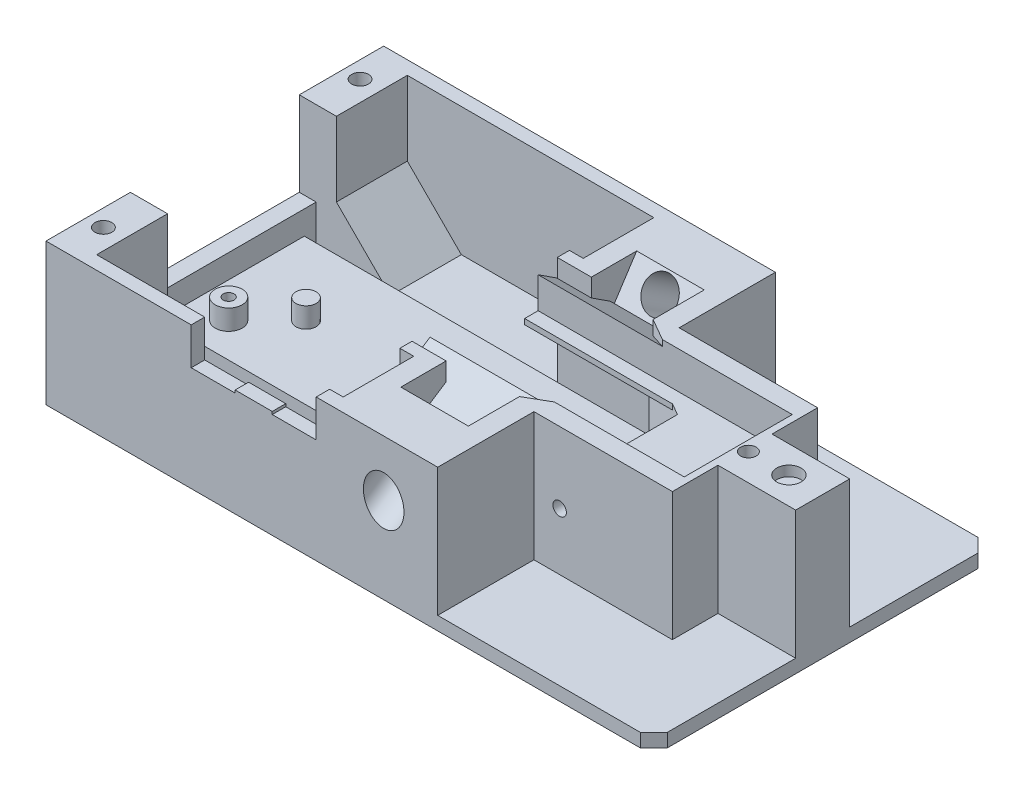
SolidWorks part; units mm, degrees
ref_plane "Front Plane" through (0, 0, 0) normal (0, 0, 1) x (1, 0, 0)
ref_plane "Top Plane" through (0, 0, 0) normal (0, 1, 0) x (1, 0, 0)
ref_plane "Right Plane" through (0, 0, 0) normal (1, 0, 0) x (0, 0, -1)
sketch "Sketch1" plane through (0, 0, 0) normal (0, 1, 0) x (1, 0, 0)
  line L0 (-111.1111, 0) -> (149.5726, 0) construction
  line L1 (0, 75.7479) -> (0, -66.1325) construction
  line L3 (-50, 25) -> (40, 25)
  line L4 (-50, 25) -> (-50, -25)
  line L5 (-50, -25) -> (40, -25)
  line L6 (40, 25) -> (40, -25)
  dimension "D1" = 50
  dimension "D2" = 40
  dimension "D3" = 50
extrude "Boss-Extrude1" add sketch "Sketch1" along normal blind 21
sketch "Sketch2" plane through (0, 21, 0) normal (0, 1, 0) x (1, 0, 0)
  line L0 (0, 0) -> (-72.5321, 0) construction
  line L1 (-44.5, 10.75) -> (3.5, 10.75)
  line L2 (-44.5, 10.75) -> (-44.5, -10.75)
  line L3 (-44.5, -10.75) -> (3.5, -10.75)
  line L4 (13.5, 5) -> (13.5, -5)
  line L5 (13.5, 5) -> (3.5, 10.75)
  line L6 (13.5, -5) -> (3.5, -10.75)
  dimension "D1" = 21.5
  dimension "D2" = 58
  dimension "D3" = 13.5
  dimension "D4" = 10
  dimension "D5" = 10
extrude "Cut-Extrude1" cut sketch "Sketch2" against normal offset from surface (16 mm away) 5 up to face at (-5, 0, 0)
sketch "Sketch3" plane through (0, 0, 0) normal (1, 0, 0) x (0, 0, -1)
  line L0 (38.5857, 3.8917) -> (0, 29) construction
  line L1 (-23.1325, 29) -> (24.9292, 29) construction
  line L2 (5, 5) -> (-5, 5) construction
  line L3 (0, 0) -> (0, 44.5037) construction
  line L4 (-25, 0) -> (25, 0) construction
  line L5 (25, 15.8341) -> (1.4181, 31.1792) construction
  line L6 (25, 9.6301) -> (-1.4181, 26.8208) construction
  line L7 (27.5121, 11.0974) -> (0, 29) construction
  line L8 (26.094, 8.9182) -> (-1.4181, 26.8208) construction
  line L9 (-18.1916, 17.5) -> (11.6037, 17.5) construction
  line L10 (7.5, -5.5044) -> (7.5, 37.9907) construction
  line L11 (28.9302, 13.2767) -> (1.4181, 31.1792) construction
  line L12 (25, 21) -> (25, 0) construction
  dimension "D1" = 24
  dimension "D4" = 12.5
  dimension "D5" = 7.5
  dimension "D2" = 2.6
  dimension "D3" = 2.6
ref_plane "Plane1" through (0, 3.8917, -38.5857) normal (0, 0.5454, 0.8382) x (1, 0, 0)
sketch "Sketch4" plane through (0, 3.8917, -38.5857) normal (0, 0.5454, 0.8382) x (1, 0, 0)
  circle A0 centre (0, 0) radius 2.5
  dimension "D1" = 5
extrude "Cut-Extrude2" cut sketch "Sketch4" along normal through all contours A0
ref_plane "Plane2" through (0, 29, 0) normal (0, 0.5454, 0.8382) x (1, 0, 0)
sketch "Sketch5" plane through (0, 29, 0) normal (0, 0.5454, 0.8382) x (1, 0, 0)
  line L0 (0, 0.0137) -> (12.9105, 0.0137) construction
  line L1 (-5, -3.0863) -> (5, -3.0863)
  line L2 (-5, -3.0863) -> (-5, 3.1137)
  line L3 (-5, 3.1137) -> (5, 3.1137)
  line L4 (5, -3.0863) -> (5, 3.1137)
  line L5 (0, -24.83) -> (0, 11.6263) construction
  line L6 (0, 0.0137) -> (0, 5.31) construction
  dimension "D1" = 6.2
  dimension "D2" = 10
extrude "Cut-Extrude3" cut sketch "Sketch5" against normal blind 19
sketch "Sketch6" plane through (0, 3.8917, -38.5857) normal (0, 0.5454, 0.8382) x (1, 0, 0)
  circle A0 centre (0, 0) radius 3
  dimension "D1" = 6
extrude "Cut-Extrude4" cut sketch "Sketch6" along normal blind 20
sketch "Sketch11" plane through (0, 5, 0) normal (0, 1, 0) x (1, 0, 0)
  line L0 (11.3, 6.265) -> (11.3, -6.265)
  line L1 (3.5, 10.75) -> (13.5, 5) construction
  line L2 (13.5, -5) -> (3.5, -10.75) construction
  line L3 (11.3, -6.265) -> (13.5, -5)
  line L4 (13.5, -5) -> (13.5, 5)
  line L6 (13.5, 5) -> (11.3, 6.265)
  line L7 (13.5, 5) -> (13.5, -5) construction
  line L8 (0, 0) -> (-46.0103, 0) construction
  circle A0 centre (-36.5, 0) radius 1.5
  dimension "D3" = 3
  dimension "D1" = 2.2
  dimension "D2" = 50
extrude "Boss-Extrude3" add sketch "Sketch11" along normal blind 3
sketch "Sketch9" plane through (13.5, 0, 0) normal (-1, 0, 0) x (0, 0, 1)
  line L1 (-25, 21) -> (25, 21) construction
  line L3 (-25, 9.6301) -> (1.4181, 26.8208) construction
  line L5 (-10.75, 5) -> (-10.75, 21) construction
  line L9 (0, 0) -> (0, 44.5037) construction
  line L12 (-8, 18.7) -> (-8, 15.5)
  line L14 (-6, 15.5) -> (-6, 14.7)
  line L20 (-8, 15.5) -> (-6, 15.5)
  line L26 (-6.265, 8) -> (6.265, 8) construction
  line L30 (-8, 18.7) -> (0, 18.7)
  line L31 (-6.6355, 21) -> (0, 21)
  line L32 (0, 21) -> (0, 18.7)
  line L34 (-11.1524, 18.0608) -> (-11.1524, 14.6627)
  line L36 (-6, 14.7) -> (-10.75, 13.6)
  line L37 (-10.75, 13.6) -> (-11.1524, 13.6)
  line L38 (-11.1524, 13.6) -> (-11.1524, 14.6627)
  line L39 (-11.1524, 18.0608) -> (-6.6355, 21)
  line L40 (-14.2419, 16.0504) -> (-10.75, 18.3226) construction
  dimension "D1" = 7.5
  dimension "D2" = 3.2
  dimension "D3" = 8
  dimension "D4" = 6
  dimension "D5" = 1.9
  dimension "D6" = 0.8
extrude "Boss-Extrude2" add sketch "Sketch9" along normal blind 23.6307
mirror "Mirror1" about plane through (0, 0, 0) normal (0, 0, 1) of "Cut-Extrude2", "Cut-Extrude3", "Boss-Extrude2", "Cut-Extrude4"
sketch "Sketch10" plane through (0, 21, 0) normal (0, 1, 0) x (1, 0, 0)
  line L1 (-44.5, 12.5) -> (-44.5, 23)
  line L2 (-8, 12.55) -> (-8, 23)
  line L4 (8, 25) -> (8, 10.75)
  line L7 (28.5, 10.75) -> (28.5, 4)
  line L8 (28.5, 4) -> (46.3281, 4)
  line L9 (46.3281, 4) -> (46.3281, 30.7176)
  line L10 (46.3281, 30.7176) -> (8, 31.0443)
  line L13 (-44.5, 23) -> (-8, 23)
  line L15 (40, 25) -> (-50, 25) construction
  line L16 (8, 25) -> (8, 31.0443)
  line L18 (-5, 17.4627) -> (-5, 10.75) construction
  line L19 (5, 9.8875) -> (5, 17.4627) construction
  line L20 (0, 0) -> (62.927, 0) construction
  line L23 (-10.0495, 12.55) -> (-10.0495, 10.75)
  line L24 (-44.5, 10.75) -> (3.5, 10.75) construction
  line L25 (-10.0495, 10.75) -> (-44.5, 10.75)
  line L26 (-10.0495, 12.55) -> (-8, 12.55)
  line L36 (-50, 25) -> (-50, -25) construction
  line L37 (-50, 12.5) -> (-50, 0)
  line L38 (-50, 0) -> (-44.5, 0)
  line L39 (-44.5, 0) -> (-44.5, 10.75)
  line L43 (-50, 12.5) -> (-44.5, 12.5)
  line L46 (8, 10.75) -> (28.5, 10.75)
  line L47 (13.5, 5) -> (13.5, -5) construction
  dimension "D1" = 12.5
  dimension "D2" = 15
  dimension "D3" = 2
  dimension "D4" = 3
  dimension "D5" = 3
  dimension "D7" = 8
extrude "Cut-Extrude6" cut sketch "Sketch10" against normal offset from surface (19 mm away) 2 contours L9 L10 L1 L43 L37 L38 L39 L25 L23 L26 L2 L4 L46 L7 L8
mirror "Mirror2" about plane through (0, 0, 0) normal (0, 0, 1) of "Cut-Extrude6"
sketch "Sketch17" plane through (-10.0495, 0, 0) normal (-1, 0, 0) x (0, 0, 1)
  line L1 (-8, 15.5) -> (8, 15.5)
  line L2 (-8, 15.5) -> (-8, 18.7)
  line L3 (-8, 18.7) -> (8, 18.7)
  line L4 (8, 15.5) -> (8, 18.7)
extrude "Cut-Extrude10" cut sketch "Sketch17" against normal offset from surface (37.5495 mm away) 1 up to face at (28.5, 11.5, 7.375)
sketch "Sketch15" plane through (0, 21, 0) normal (0, 1, 0) x (1, 0, 0)
  line L2 (-50, 25) -> (-50, 12.5) construction
  circle A0 centre (35, 0) radius 1.8
  dimension "D1" = 3.6
  dimension "D2" = 85
extrude "Cut-Extrude8" cut sketch "Sketch15" against normal blind 1.5
sketch "Sketch16" plane through (0, 21, 0) normal (0, 1, 0) x (1, 0, 0)
  line L0 (-47.5, 19) -> (-47.5, -19) construction
  line L2 (-50, 25) -> (-50, 12.5) construction
  line L4 (0, 0) -> (-66.2156, 0) construction
  circle A0 centre (-47.5, 19) radius 1.25
  circle A1 centre (-47.5, -19) radius 1.25
  dimension "D1" = 2.5
  dimension "D2" = 38
  dimension "D3" = 2.5
extrude "Cut-Extrude9" cut sketch "Sketch16" against normal up to surface (19 mm away)
sketch "Sketch19" plane through (0, 21, 0) normal (0, 1, 0) x (1, 0, 0)
  circle A0 centre (0, 0) radius 4
  dimension "D1" = 8
extrude "Cut-Extrude11" cut sketch "Sketch19" against normal up to next
chamfer "Chamfer1" distance 8 angle 45 2 edges at (-44.5, 2, -17.75) (-44.5, 2, 17.75)
chamfer "Chamfer2" distance 2 angle 45 2 edges at (40, 1, -25) (40, 1, 25)
sketch "Sketch20" plane through (0, 0, 25) normal (0, 0, 1) x (1, 0, 0)
  line L3 (-28.5, 15.5) -> (-22, 15.5)
  line L4 (-10, 21) -> (-10, 15.5)
  line L5 (-28.5, 21) -> (-10, 21)
  line L9 (40, 2) -> (40, 21) construction
  line L10 (-28.5, 15.8) -> (-28.5, 21)
  line L12 (-16.5, 15.5) -> (-16.5, 15.9)
  line L13 (-16.5, 15.9) -> (-22, 15.9)
  line L14 (-22, 15.9) -> (-22, 15.5)
  line L15 (-28.5, 15.5) -> (-28.5, 15.8)
  line L17 (-16.5, 15.5) -> (-10, 15.5)
  point P17 (-22, 15.7)
  dimension "D1" = 5.5
  dimension "D2" = 0.4
  dimension "D3" = 6.5
  dimension "D4" = 6.5
  dimension "D5" = 50
  dimension "D6" = 5.5
extrude "Cut-Extrude12" cut sketch "Sketch20" against normal up to next
sketch "Sketch21" plane through (-44.5, 0, 0) normal (-1, 0, 0) x (0, 0, 1)
  line L0 (10.75, 2) -> (10.75, 5) construction
  line L1 (-10.75, 5) -> (10.75, 5)
  line L2 (-10.75, 5) -> (-10.75, 2)
  line L3 (-10.75, 2) -> (10.75, 2)
  line L4 (10.75, 5) -> (10.75, 2)
  line L5 (12.55, 2) -> (10.75, 2) construction
extrude "Boss-Extrude4" add sketch "Sketch21" along normal up to surface (5.5 mm away) up to face at (-50, 11, 0)
sketch "Sketch22" plane through (0, 5, 0) normal (0, 1, 0) x (1, 0, 0)
  line L1 (0, 0) -> (-47.0213, 0) construction
  line L2 (13.5, -5) -> (13.5, 5) construction
  circle A0 centre (-42.3, -5.65) radius 2
  circle A1 centre (-42.3, -5.65) radius 0.8
  circle A2 centre (9.66, 4.95) radius 2
  circle A3 centre (9.66, 4.95) radius 0.8
  dimension "D1" = 1.6
  dimension "D2" = 4
  dimension "D5" = 3.84
  dimension "D3" = 55.8
  dimension "D4" = 5.65
  dimension "D6" = 4.95
sketch "Sketch23" plane through (0, 21, 0) normal (0, 1, 0) x (1, 0, 0)
  line L0 (27.5, 8) -> (-10.1307, 8)
  line L1 (-10.1307, 8) -> (27.5, 8) construction
  line L2 (-10.1307, 8) -> (-10.1307, -8)
  line L3 (-10.1307, -8) -> (27.5, -8)
  line L4 (27.5, -8) -> (27.5, 8)
extrude "Cut-Extrude13" cut sketch "Sketch23" against normal up to next
sketch "Sketch24" plane through (0, 21, 0) normal (0, 1, 0) x (1, 0, 0)
  line L0 (-50, 25) -> (8, 25)
  line L1 (8, 25) -> (8, 10.75)
  line L2 (8, 10.75) -> (28.5, 10.75)
  line L3 (28.5, 10.75) -> (28.5, 4)
  line L4 (28.5, 4) -> (28.5, 10.75) construction
  line L5 (28.5, 4) -> (32.5275, 4)
  line L6 (28.5, 4) -> (40, 4) construction
  line L7 (32.5275, 4) -> (32.5275, -4)
  line L8 (28.5, -4) -> (40, -4) construction
  line L9 (32.5275, -4) -> (28.5, -4)
  line L10 (28.5, -4) -> (28.5, -10.75)
  line L11 (28.5, -10.75) -> (8, -10.75)
  line L12 (8, -10.75) -> (8, -25)
  line L13 (8, -25) -> (-50, -25)
  line L14 (-50, -25) -> (-50, 25)
  line L15 (-5, 17.4627) -> (-5, -17.4627)
  line L16 (-5, -17.4627) -> (5, -17.4627)
  line L17 (5, -17.4627) -> (5, 17.4627)
  line L18 (5, 17.4627) -> (-5, 17.4627)
  line L19 (-5, 6) -> (5, 6)
  line L20 (-10.1307, 6) -> (11.7609, 6) construction
  line L21 (-5, -6) -> (5, -6)
  line L22 (-10.1307, -6) -> (11.7609, -6) construction
  line L23 (-10.1307, 8) -> (27.5, 8)
  line L24 (27.5, 8) -> (27.5, -8)
  line L25 (27.5, -8) -> (-10.1307, -8)
  line L26 (8.2826, -8) -> (-10.1307, -8) construction
  line L27 (-10.1307, -8) -> (27.5, -8) construction
  line L28 (-42.7423, -23) -> (-8, -23)
sketch "Sketch25" plane through (0, 21, 0) normal (0, 1, 0) x (1, 0, 0)
  line L0 (40, -4) -> (40, 4) construction
  circle A0 centre (29, 0) radius 1.15
  dimension "D1" = 2.3
  dimension "D2" = 11
extrude "Cut-Extrude14" cut sketch "Sketch25" against normal blind 10
sketch "Sketch26" plane through (0, 0, 10.75) normal (0, 0, 1) x (1, 0, 0)
  circle A0 centre (11.8025, 10.4715) radius 1
  dimension "D1" = 2
extrude "Cut-Extrude15" cut sketch "Sketch26" against normal through all
sketch "Sketch27" plane through (0, 2, 0) normal (0, 1, 0) x (1, 0, 0)
  line L1 (-50, 12.5) -> (-47.5, 12.5)
  line L2 (-50, 12.5) -> (-50, -12.5)
  line L3 (-50, -12.5) -> (-47.5, -12.5)
  line L4 (-47.5, 12.5) -> (-47.5, -12.5)
  dimension "D1" = 2.5
extrude "Boss-Extrude6" add sketch "Sketch27" along normal blind 6.5
sketch "Sketch28" plane through (0, 17.7865, 11.5739) normal (0, 0.8382, 0.5454) x (1, 0, 0)
  line L0 (5, -3.1831) -> (5, 2.0121) construction
  line L1 (-5, -3.1831) -> (5, -3.1831)
  line L2 (-5, -3.1831) -> (-5, -2.3831)
  line L3 (-5, -2.3831) -> (5, -2.3831)
  line L4 (5, -3.1831) -> (5, -2.3831)
  dimension "D1" = 0.8
extrude "Cut-Extrude16" cut sketch "Sketch28" against normal blind 4
mirror "Mirror3" about plane through (0, 0, 0) normal (0, 0, 1) of "Cut-Extrude16"
extrude "Boss-Extrude7" add sketch "Sketch22" along normal up to surface (3 mm away) up to face at (-36.5, 8, 1.5)
